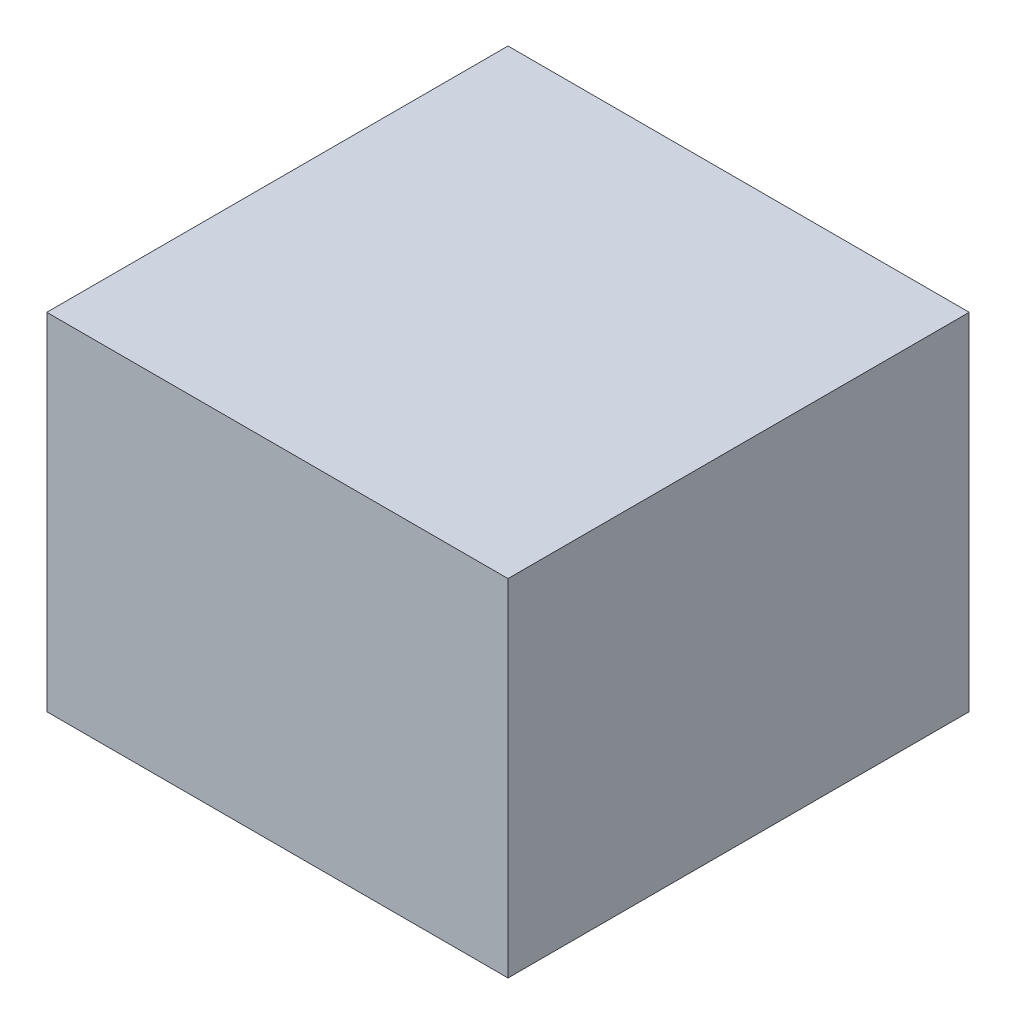
SolidWorks part; units mm, degrees
ref_plane "Front Plane" through (0, 0, 0) normal (0, 0, 1) x (1, 0, 0)
ref_plane "Top Plane" through (0, 0, 0) normal (0, 1, 0) x (1, 0, 0)
ref_plane "Right Plane" through (0, 0, 0) normal (1, 0, 0) x (0, 0, -1)
sketch "Sketch1" plane through (0, 0, 0) normal (0, 1, 0) x (1, 0, 0)
  line L1 (-10, -10) -> (10, -10)
  line L2 (-10, -10) -> (-10, 10)
  line L3 (-10, 10) -> (10, 10)
  line L4 (10, -10) -> (10, 10)
  line L5 (-10, -10) -> (10, 10) construction
  line L6 (-10, 10) -> (10, -10) construction
  point P0 (0, 0)
extrude "Boss-Extrude1" add sketch "Sketch1" along normal blind 15
